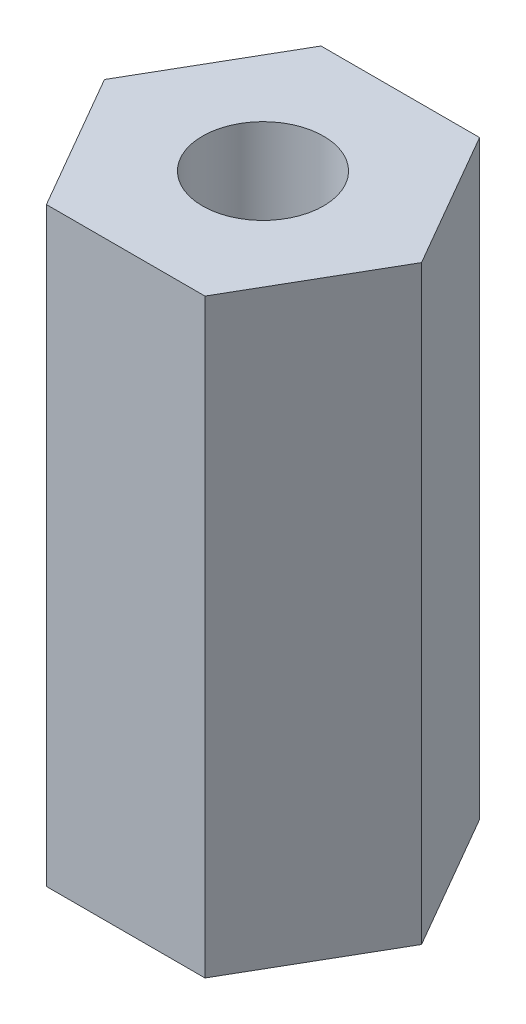
SolidWorks part; units mm, degrees
material "Brass"
ref_plane "Front Plane" through (0, 0, 0) normal (0, 0, 1) x (1, 0, 0)
ref_plane "Top Plane" through (0, 0, 0) normal (0, 1, 0) x (1, 0, 0)
ref_plane "Right Plane" through (0, 0, 0) normal (1, 0, 0) x (0, 0, -1)
sketch "Sketch1" plane through (0, 0, 0) normal (0, 1, 0) x (1, 0, 0)
  line L1 (2.6847, 0) -> (1.3423, 2.325)
  line L2 (1.3423, 2.325) -> (-1.3423, 2.325)
  line L3 (-1.3423, 2.325) -> (-2.6847, 0)
  line L4 (-2.6847, 0) -> (-1.3423, -2.325)
  line L5 (-1.3423, -2.325) -> (1.3423, -2.325)
  line L6 (1.3423, -2.325) -> (2.6847, 0)
  circle A0 centre (0, 0) radius 2.325 construction
  dimension "D1" = 4.65
extrude "Boss-Extrude1" add sketch "Sketch1" along normal blind 10
hole_wizard "M2.5x0.45 Tapped Hole1" positions "Sketch2" profile "Sketch3" tap size "M2.5x0.45" standard "ANSI Metric"
sketch "Sketch2" plane through (0, 10, 0) normal (0, 1, 0) x (1, 0, 0)
  point P0 (0, 0)
sketch "Sketch3" plane through (0, 10, 0) normal (1, 0, 0) x (0, 0, 1)
  line L0 (0, 0) -> (0, 25.6159)
  line L1 (0, 25.6159) -> (1.025, 25)
  line L2 (1.025, 25) -> (1.025, 0)
  line L5 (1.025, 0) -> (0, 0)
  line L10 (0, 25.6159) -> (-1.025, 25) construction
  line L11 (0, -6.35) -> (0, 107.95) construction
  dimension "Tap Drill Dia." = 2.05
  dimension "Tap Drill Depth" = 25
  dimension "Drill Angle" = 118
cosmetic thread "Hole Thread1" parameters "D1"=5, "D2"=2.5
